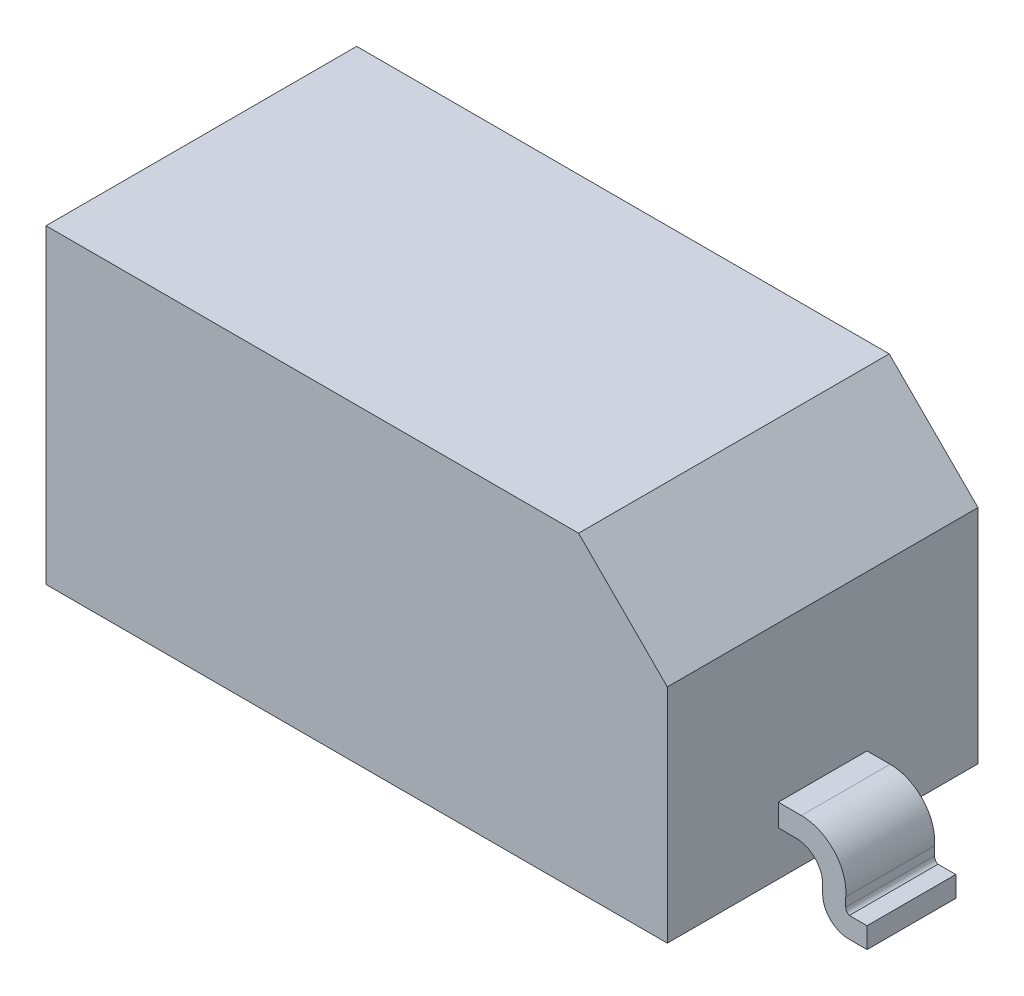
SolidWorks part; units mm, degrees
ref_plane "Front Plane" through (0, 0, 0) normal (0, 0, 1) x (1, 0, 0)
ref_plane "Top Plane" through (0, 0, 0) normal (0, 1, 0) x (1, 0, 0)
ref_plane "Right Plane" through (0, 0, 0) normal (1, 0, 0) x (0, 0, -1)
sketch "Sketch1" plane through (0, 0, 0) normal (0, 0, 1) x (1, 0, 0)
  line L0 (-1.75, -0.875) -> (1.75, -0.875)
  line L1 (1.75, -0.875) -> (1.75, 0.375)
  line L2 (1.75, 0.375) -> (1.25, 0.875)
  line L3 (1.25, 0.875) -> (-1.75, 0.875)
  line L4 (-1.75, 0.875) -> (-1.75, -0.875)
  line L5 (0, -0.875) -> (0, 0.875) construction
  dimension "D1" = 3
  dimension "D2" = 3.5
  dimension "D3" = 1.75
  dimension "D4" = 1.25
  dimension "D5" = 45
extrude "Extrude1" add sketch "Sketch1" along normal mid plane 1.75
sketch "Sketch2" plane through (0, 0, 0) normal (0, 0, 1) x (1, 0, 0)
  line L0 (1.75, -0.625) -> (1.85, -0.625)
  line L1 (1.75, -0.875) -> (1.75, 0.375) construction
  line L2 (-1.75, -0.875) -> (1.75, -0.875) construction
  line L3 (1.75, -0.625) -> (1.75, -0.4995)
  line L4 (1.75, -0.4995) -> (1.88, -0.4995)
  line L5 (2, -0.772) -> (2, -0.822)
  line L6 (2.13, -0.7722) -> (2.13, -0.8222)
  line L7 (2.15, -0.8522) -> (2.25, -0.8522)
  line L8 (2.25, -0.8522) -> (2.25, -0.9689)
  line L9 (2.25, -0.9689) -> (2.15, -0.9689)
  arc A0 (1.85, -0.625) -> (2, -0.772) centre (1.85, -0.775) cw
  arc A1 (1.88, -0.4995) -> (2.13, -0.7722) centre (1.88, -0.7504) cw
  arc A2 (2, -0.822) -> (2.15, -0.9689) centre (2.147, -0.822) ccw
  arc A3 (2.13, -0.8222) -> (2.15, -0.8522) centre (2.1625, -0.8222) ccw
  dimension "D4" = 0.21
  dimension "D5" = 0.15
  dimension "D12" = 0.03
  dimension "D1" = 0.25
  dimension "D2" = 0.13
  dimension "D3" = 0.1
  dimension "D6" = 0.37
  dimension "D7" = 0.1255
  dimension "D8" = 0.25
  dimension "D9" = 0.21
  dimension "D10" = 0.15
  dimension "D11" = 0.05
  dimension "D13" = 0.1
extrude "Extrude2" add sketch "Sketch2" along normal mid plane 0.5
mirror "Mirror1" about plane through (0, 0, 0) normal (1, 0, 0) of "Extrude2"
